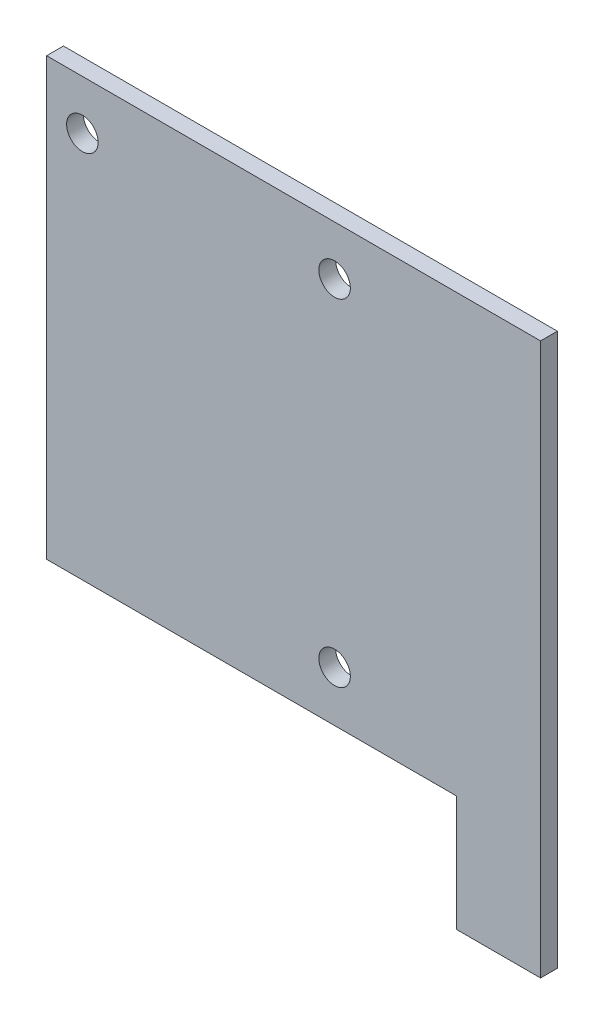
SolidWorks part; units mm, degrees
ref_plane "前视基准面" through (0, 0, 0) normal (0, 0, 1) x (1, 0, 0)
ref_plane "上视基准面" through (0, 0, 0) normal (0, 1, 0) x (1, 0, 0)
ref_plane "右视基准面" through (0, 0, 0) normal (1, 0, 0) x (0, 0, -1)
sketch "草图1" plane through (0, 0, 0) normal (0, 0, 1) x (1, 0, 0)
  line L0 (0, 0) -> (19721.0696, 0) construction
  line L1 (0, 0) -> (0, 19721.0696) construction
  line L2 (15.5, -26.25) -> (15.5, -15.25)
  line L3 (-23.5, 26.25) -> (23.5, 26.25)
  line L4 (-23.5, 26.25) -> (-23.5, -15.25)
  line L5 (15.5, -26.25) -> (23.5, -26.25)
  line L6 (23.5, 26.25) -> (23.5, -26.25)
  line L7 (15.5, -15.25) -> (-23.5, -15.25)
  circle A0 centre (3.9, 21.55) radius 1.5
  circle A1 centre (3.9, -10.45) radius 1.5
  circle A2 centre (-20.1, 21.55) radius 1.5
  dimension "D3" = 3
  dimension "D4" = 24
  dimension "D5" = 32
  dimension "D6" = 3.4
  dimension "D7" = 4.7
  dimension "D1" = 52.5
  dimension "D2" = 47
  dimension "D8" = 8
  dimension "D9" = 11
extrude "凸台-拉伸1" add sketch "草图1" along normal blind 1.6
